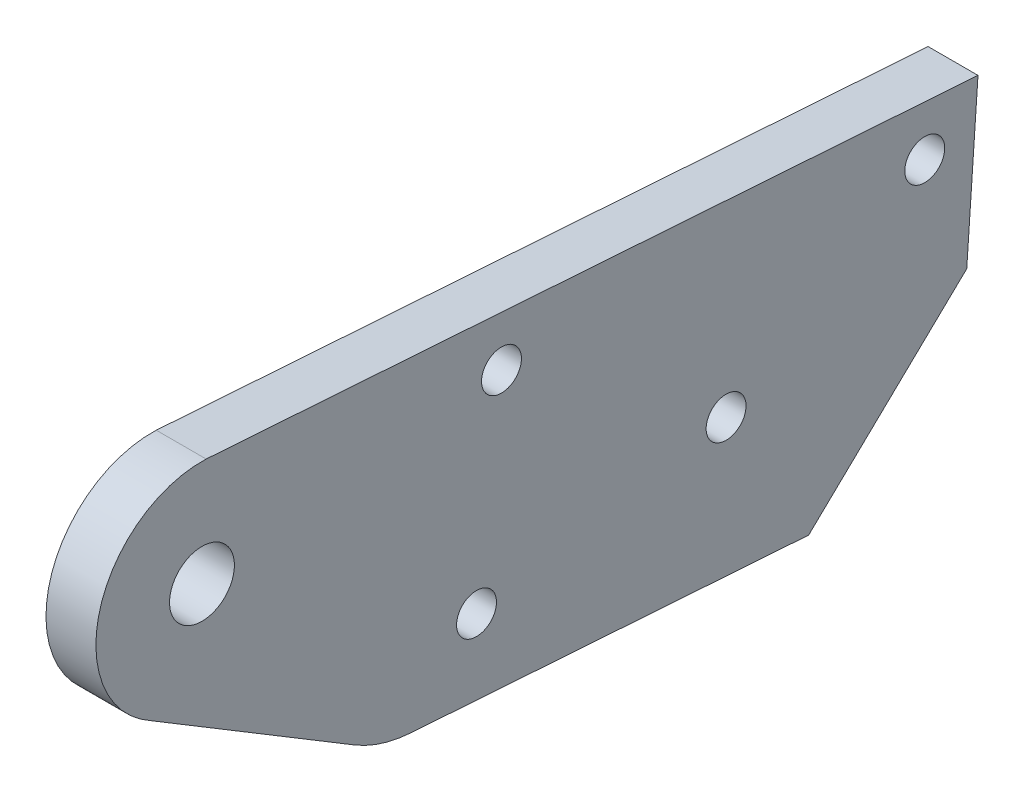
SolidWorks part; units mm, degrees
ref_plane "前视基准面" through (0, 0, 0) normal (0, 0, 1) x (1, 0, 0)
ref_plane "上视基准面" through (0, 0, 0) normal (0, 1, 0) x (1, 0, 0)
ref_plane "右视基准面" through (0, 0, 0) normal (1, 0, 0) x (0, 0, -1)
sketch "草图1" plane through (0, 0, 0) normal (1, 0, 0) x (0, 0, -1)
  line L0 (15.9615, -1.1096) -> (28.63, 11.041)
  line L1 (29.5316, 24.0097) -> (-32.3191, 28.3095)
  line L2 (29.5316, 24.0097) -> (28.63, 11.041)
  line L3 (15.9615, -1.1096) -> (-15.9615, 1.1096)
  line L10 (-20.4336, 2.5231) -> (-36.7795, 12.3843)
  circle A0 centre (25.2638, 20.2968) radius 1.6
  circle A1 centre (-8.6543, 22.6547) radius 1.6
  arc A2 (-32.3191, 28.3095) -> (-36.7795, 12.3843) centre (-32.6543, 19.8162) ccw
  circle A3 centre (9.3457, 10.3768) radius 1.6
  circle A4 centre (-10.6543, 6.7552) radius 1.6
  circle A5 centre (-32.6543, 19.8162) radius 2.6
  arc A6 (-15.9615, 1.1096) -> (-20.4336, 2.5231) centre (-15.268, 11.0855) cw
  point P0 (-150, 0)
  point P1 (135, 0)
  point P9 (-344.9533, 138.7825)
  point P10 (187.1329, 101.1747)
  point P11 (165.9429, -19)
  point P12 (-156.9154, -19)
  dimension "D7" = 13
  dimension "D8" = 32
  dimension "D9" = 24
  dimension "D10" = 26
  dimension "D4" = 22
  dimension "D11" = 4
  dimension "D12" = 26
  dimension "D13" = 16
  dimension "D14" = 90
  dimension "D15" = 132.219
  dimension "D16" = 62
  dimension "D17" = 8.5
  dimension "D19" = 34
  dimension "D20" = 3.2
  dimension "D6" = 11
  dimension "D5" = 6
  dimension "D21" = 4
  dimension "D22" = 3.2
  dimension "D23" = 3.2
  dimension "D24" = 3.2
  dimension "D28" = 10
  dimension "D3" = 4
  dimension "D26" = 20
  dimension "D27" = 5.2
extrude "凸台-拉伸1" add sketch "草图1" along normal blind 4
